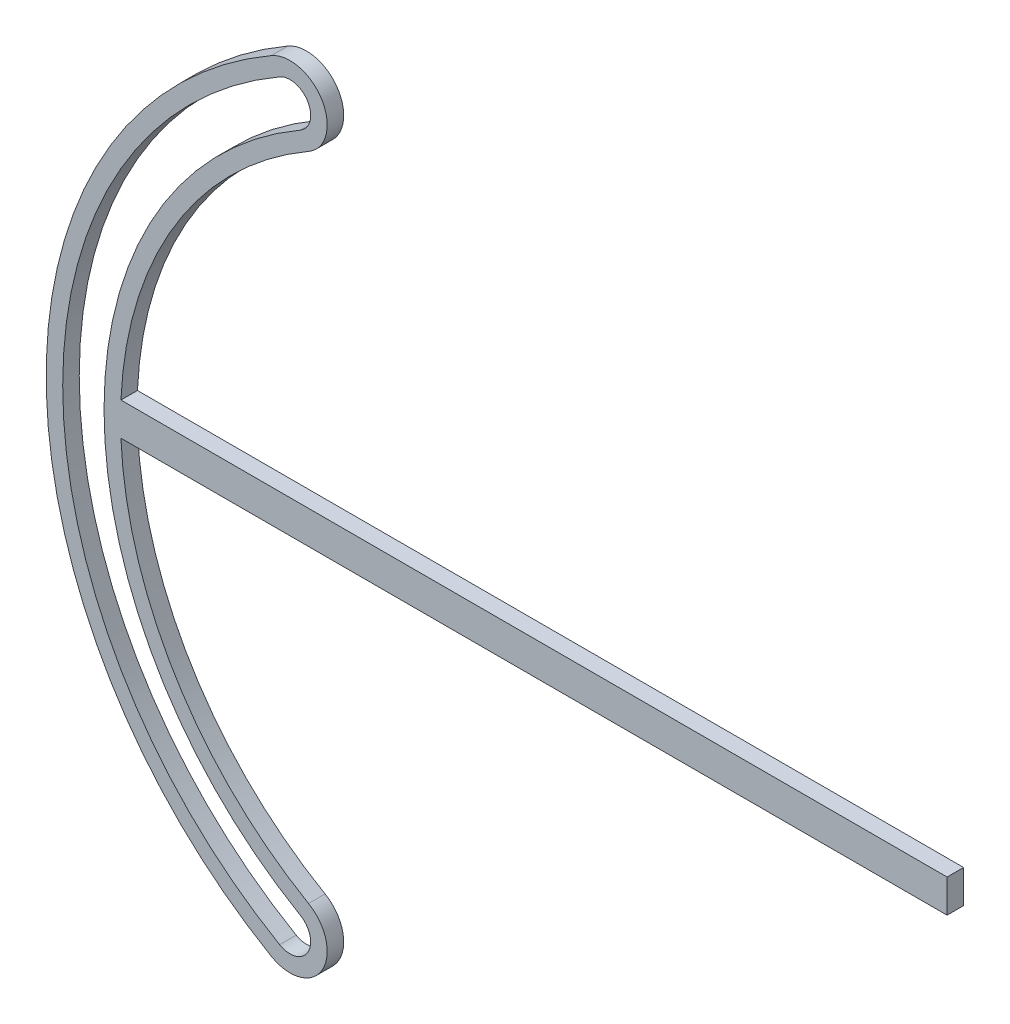
SolidWorks part; units mm, degrees
ref_plane "前视基准面" through (0, 0, 0) normal (0, 0, 1) x (1, 0, 0)
ref_plane "上视基准面" through (0, 0, 0) normal (0, 1, 0) x (1, 0, 0)
ref_plane "右视基准面" through (0, 0, 0) normal (1, 0, 0) x (0, 0, -1)
sketch "草图1" plane through (0, 0, 0) normal (0, 0, 1) x (1, 0, 0)
  line L2 (0, -4) -> (-91, -4)
  line L3 (0, -4) -> (109, -4)
  line L4 (0, 4) -> (-91, 4)
  line L5 (0, 4) -> (109, 4)
  line L6 (109, 4) -> (109, -4)
  arc A0 (-90.912, -4) -> (-45.5, -78.8083) centre (0, 0) ccw
  arc A1 (-52.5, 90.9327) -> (-52.5, -90.9327) centre (0, 0) ccw
  arc A2 (-47.5, 82.2724) -> (-47.5, -82.2724) centre (0, 0) ccw
  arc A3 (-54.5, 94.3968) -> (-54.5, -94.3968) centre (0, 0) ccw
  arc A4 (-45.5, 78.8083) -> (-90.912, 4) centre (0, 0) ccw
  arc A5 (-52.5, -90.9327) -> (-47.5, -82.2724) centre (-50, -86.6025) ccw
  arc A7 (-54.5, -94.3968) -> (-45.5, -78.8083) centre (-50, -86.6025) ccw
  arc A8 (-47.5, 82.2724) -> (-52.5, 90.9327) centre (-50, 86.6025) ccw
  arc A9 (-45.5, 78.8083) -> (-54.5, 94.3968) centre (-50, 86.6025) ccw
extrude "凸台-拉伸1" add sketch "草图1" along normal blind 4
